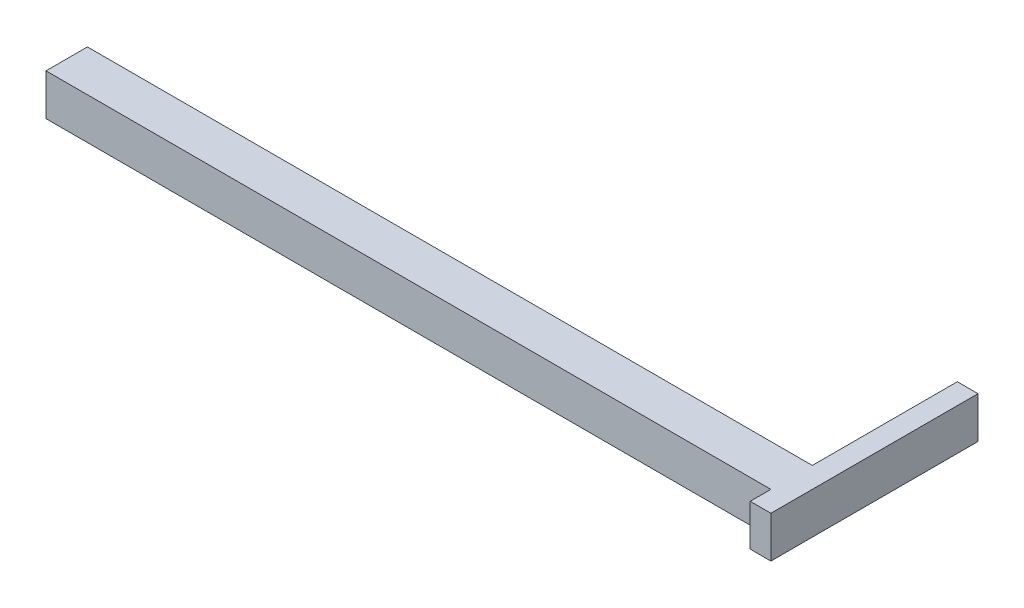
SolidWorks part; units mm, degrees
ref_plane "Alzado" through (0, 0, 0) normal (0, 0, 1) x (1, 0, 0)
ref_plane "Planta" through (0, 0, 0) normal (0, 1, 0) x (1, 0, 0)
ref_plane "Vista lateral" through (0, 0, 0) normal (1, 0, 0) x (0, 0, -1)
sketch "Croquis1" plane through (0, 0, 0) normal (0, 0, 1) x (1, 0, 0)
  line L1 (1750, -100) -> (-1750, -100)
  line L2 (1750, -100) -> (1750, 100)
  line L3 (1750, 100) -> (-1750, 100)
  line L4 (-1750, -100) -> (-1750, 100)
  line L5 (1750, -100) -> (-1750, 100) construction
  line L6 (1750, 100) -> (-1750, -100) construction
  point P0 (0, 0)
  dimension "D1" = 3500
  dimension "D2" = 200
extrude "Saliente-Extruir1" add sketch "Croquis1" along normal blind 200
sketch "Croquis2" plane through (1750, 0, 0) normal (1, 0, 0) x (0, 0, -1)
  line L1 (0, 100) -> (-300, 100)
  line L3 (0, -100) -> (-300, -100)
  line L4 (-300, 100) -> (-300, -100)
  line L5 (0, -100) -> (700, -100)
  line L7 (0, 100) -> (700, 100)
  line L8 (700, -100) -> (700, 100)
  dimension "D1" = 300
  dimension "D2" = 700
extrude "Saliente-Extruir2" add sketch "Croquis2" along normal blind 100
